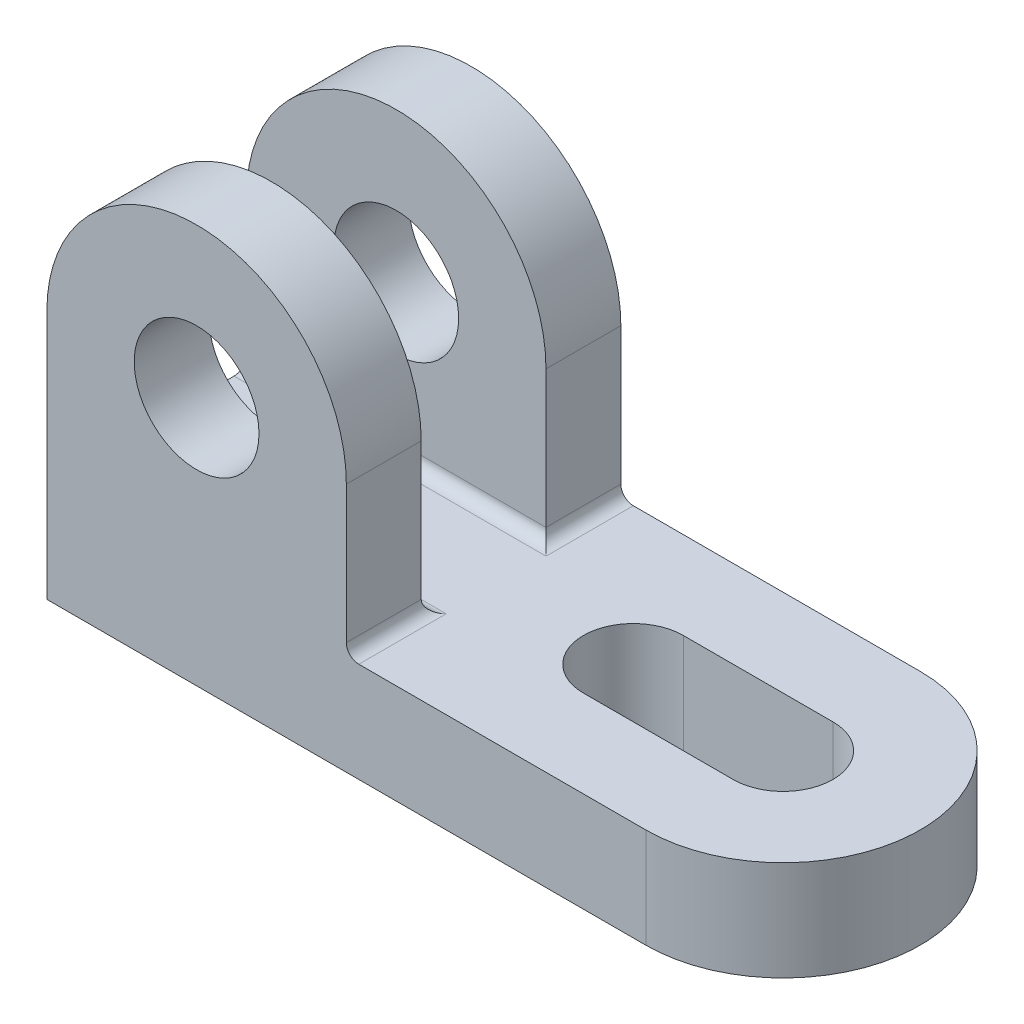
SolidWorks part; units mm, degrees
ref_plane "Front Plane" through (0, 0, 0) normal (0, 0, 1) x (1, 0, 0)
ref_plane "Top Plane" through (0, 0, 0) normal (0, 1, 0) x (1, 0, 0)
ref_plane "Right Plane" through (0, 0, 0) normal (1, 0, 0) x (0, 0, -1)
sketch "Sketch1" plane through (0, 0, 0) normal (0, 1, 0) x (1, 0, 0)
  line L1 (-59, 22) -> (59, 22)
  line L2 (-59, 22) -> (-59, -22)
  line L3 (-59, -22) -> (59, -22)
  line L4 (59, 22) -> (59, -22)
  line L5 (-59, 22) -> (59, -22) construction
  line L6 (-59, -22) -> (59, 22) construction
  circle A0 centre (37, 0) radius 22
  point P0 (0, 0)
  dimension "D1" = 118
  dimension "D2" = 44
extrude "Boss-Extrude1" add sketch "Sketch1" along normal blind 16 contours A0 L1 L2 L3 | A0
sketch "Sketch2" plane through (0, 16, 0) normal (0, 1, 0) x (1, 0, 0)
  line L0 (37, 0) -> (13, 0) construction
  line L1 (37, -8) -> (13, -8)
  line L2 (37, 8) -> (13, 8)
  arc A0 (37, -8) -> (37, 8) centre (37, 0) ccw
  arc A1 (13, 8) -> (13, -8) centre (13, 0) ccw
  point P4 (25, 0)
  dimension "D2" = 8
  dimension "D1" = 24
extrude "Cut-Extrude1" cut sketch "Sketch2" against normal blind 16
sketch "Sketch3" plane through (0, 0, 22) normal (0, 0, 1) x (1, 0, 0)
  line L0 (-59, 0) -> (37, 0) construction
  line L1 (-59, 16) -> (-11, 16)
  line L2 (-59, 16) -> (-59, 40)
  line L3 (-59, 40) -> (-11, 40)
  line L4 (-11, 16) -> (-11, 40)
  circle A0 centre (-35, 40) radius 24
  circle A1 centre (-35, 40) radius 10
  dimension "D3" = 20
  dimension "D1" = 40
  dimension "D2" = 48
extrude "Boss-Extrude2" add sketch "Sketch3" against normal blind 12 contours A0 L2 L4 | A0 L2 L1 | A1 L3 A0 | A1 L3 A0
mirror "Mirror1" about plane through (0, 0, 0) normal (0, 0, 1) of "Boss-Extrude2"
fillet "Fillet1" radius 2 4 edges at (-35, 16, -10) (-35, 16, 10) (-11, 16, -16) (-11, 16, 16)
